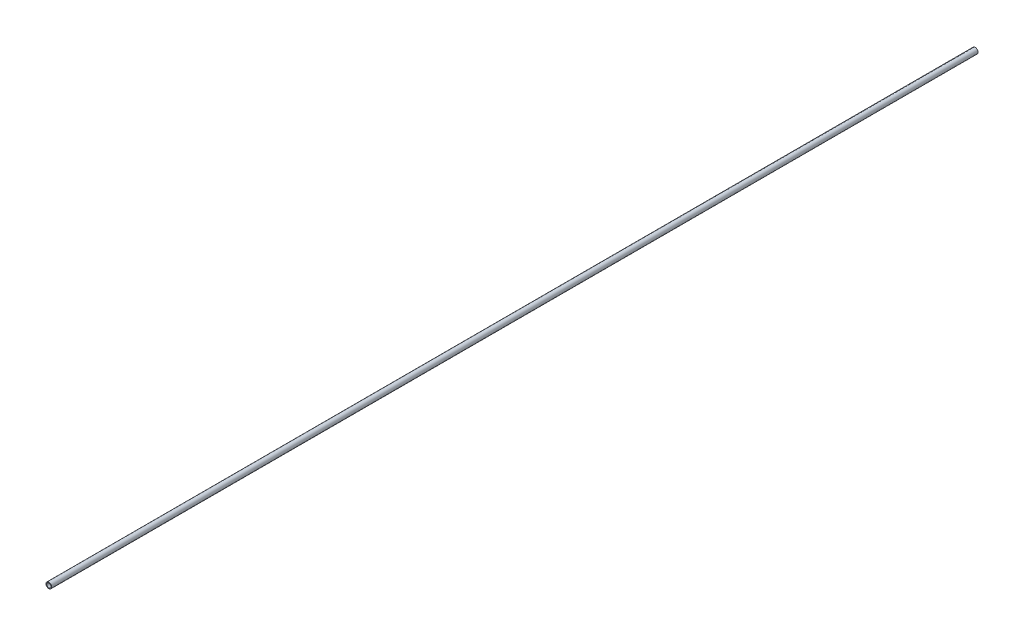
SolidWorks part; units mm, degrees
ref_plane "Front Plane" through (0, 0, 0) normal (0, 0, 1) x (1, 0, 0)
ref_plane "Top Plane" through (0, 0, 0) normal (0, 1, 0) x (1, 0, 0)
ref_plane "Right Plane" through (0, 0, 0) normal (1, 0, 0) x (0, 0, -1)
sketch "Sketch1" plane through (0, 0, 0) normal (0, 0, 1) x (1, 0, 0)
  circle A0 centre (0, 0) radius 10.668
  dimension "Pipe OD" = 21.336
extrude "Extrude-Thin1" add sketch "Sketch1" along normal mid plane 3500 thin thin type one direction reverse wall 2.7686
